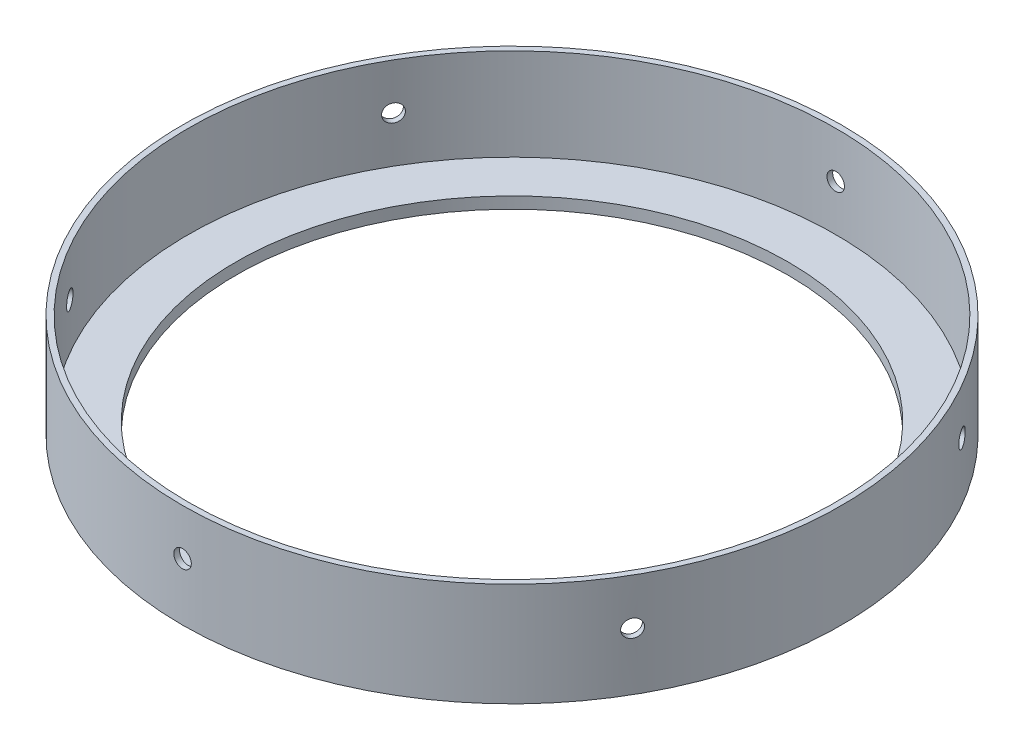
SolidWorks part; units mm, degrees
ref_plane "Front Plane" through (0, 0, 0) normal (0, 0, 1) x (1, 0, 0)
ref_plane "Top Plane" through (0, 0, 0) normal (0, 1, 0) x (1, 0, 0)
ref_plane "Right Plane" through (0, 0, 0) normal (1, 0, 0) x (0, 0, -1)
sketch "Sketch1" plane through (0, 0, 0) normal (0, 1, 0) x (1, 0, 0)
  circle A0 centre (0, 0) radius 90.8844
  dimension "D1" = 181.7688
extrude "Boss-Extrude1" add sketch "Sketch1" along normal blind 28.575
sketch "Sketch2" plane through (0, 28.575, 0) normal (0, 1, 0) x (1, 0, 0)
  circle A0 centre (0, 0) radius 90.8844 construction
  circle A1 centre (0, 0) radius 90.8844 construction
  circle A2 centre (0, 0) radius 89.2969
  dimension "D1" = 178.5938
extrude "Cut-Extrude1" cut sketch "Sketch2" against normal blind 25.4
sketch "Sketch3" plane through (0, 3.175, 0) normal (0, 1, 0) x (1, 0, 0)
  circle A0 centre (0, 0) radius 76.2
  dimension "D1" = 152.4
extrude "Cut-Extrude2" cut sketch "Sketch3" against normal through all
sketch "Sketch4" plane through (0, 0, 0) normal (0, 0, 1) x (1, 0, 0)
  line L0 (0, 28.575) -> (0, 15.875) construction
  line L1 (89.2969, 28.575) -> (-89.2969, 28.575) construction
  circle A0 centre (0, 15.875) radius 2.413
  dimension "D2" = 4.826
  dimension "D1" = 12.7
extrude "Cut-Extrude3" cut sketch "Sketch4" against normal through all both and the other way through all
pattern_circular "CirPattern1" count 6 over 360 about axis through (0, 28.575, 0) along (0, 1, 0) of "Cut-Extrude3"
